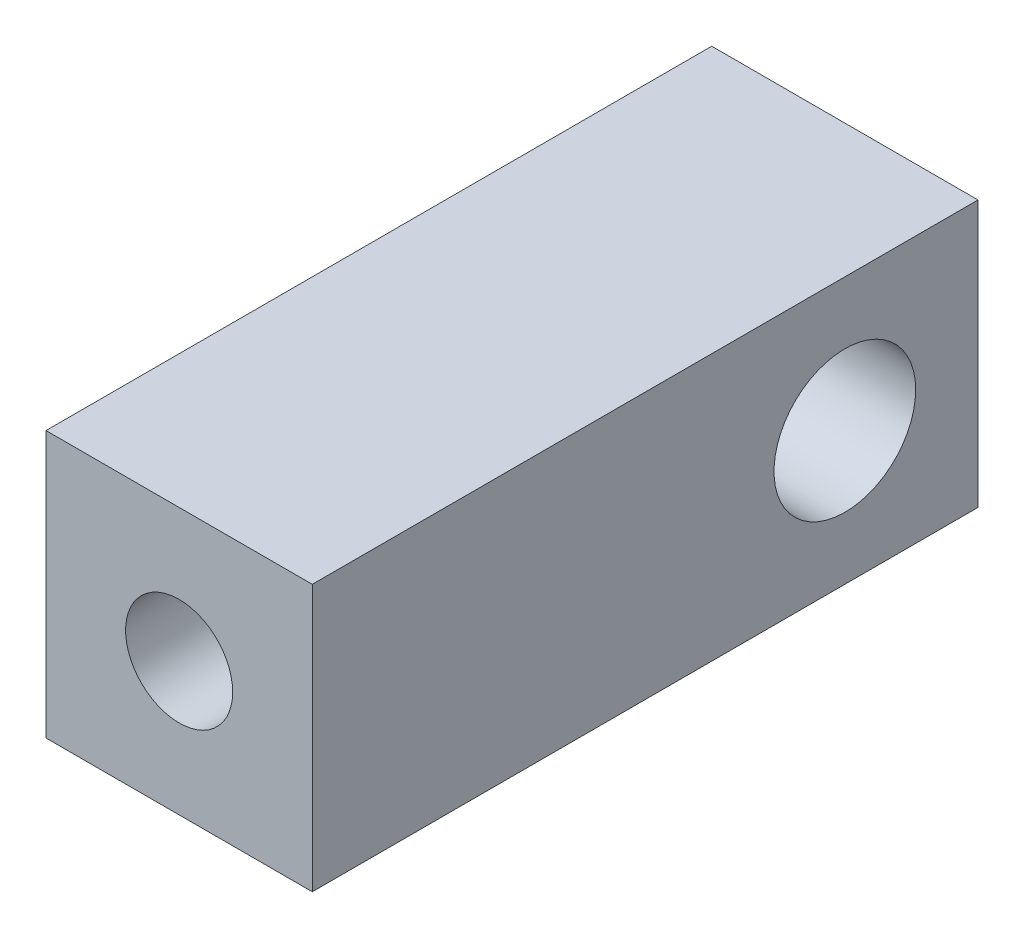
SolidWorks part; units mm, degrees
material "6061-T6 (SS)"
ref_plane "Front Plane" through (0, 0, 0) normal (0, 0, 1) x (1, 0, 0)
ref_plane "Top Plane" through (0, 0, 0) normal (0, 1, 0) x (1, 0, 0)
ref_plane "Right Plane" through (0, 0, 0) normal (1, 0, 0) x (0, 0, -1)
sketch "Sketch1" plane through (0, 0, 0) normal (1, 0, 0) x (0, 0, -1)
  line L1 (0, 0) -> (31.75, 0)
  line L2 (0, 0) -> (0, 12.7)
  line L3 (0, 12.7) -> (31.75, 12.7)
  line L4 (31.75, 0) -> (31.75, 12.7)
  dimension "D1" = 12.7
  dimension "D2" = 31.75
extrude "Boss-Extrude1" add sketch "Sketch1" along normal blind 12.7
hole_wizard "1/4-20 Tapped Hole1" positions "Sketch2" profile "Sketch3" tap size "1/4-20" standard "ANSI Inch"
sketch "Sketch2" plane through (0, 0, 0) normal (0, 0, 1) x (1, 0, 0)
  line L0 (0, 0) -> (12.7, 12.7) construction
  point P0 (6.35, 6.35)
cosmetic thread "Hole Thread1" parameters "D1"=12.7, "D2"=6.35
sketch "Sketch3" plane through (6.35, 6.35, 0) normal (1, 0, 0) x (0, -1, 0)
  line L0 (0, 0) -> (0, 18.0438)
  line L1 (0, 18.0438) -> (2.5527, 16.51)
  line L2 (2.5527, 16.51) -> (2.5527, 0)
  line L5 (2.5527, 0) -> (0, 0)
  line L10 (0, 18.0438) -> (-2.5527, 16.51) construction
  line L11 (0, -6.35) -> (0, 107.95) construction
  dimension "Tap Drill Dia." = 5.1054
  dimension "Tap Drill Depth" = 16.51
  dimension "Drill Angle" = 118
sketch "Sketch4" plane through (12.7, 0, 0) normal (1, 0, 0) x (0, 0, -1)
  line L0 (31.75, 0) -> (31.75, 12.7) construction
  line L1 (0, 12.7) -> (0, 0) construction
  circle A0 centre (25.4, 6.35) radius 3.3782
  point P7 (0, 6.35)
  dimension "D1" = 6.35
  dimension "D2" = 6.7564
extrude "Cut-Extrude1" cut sketch "Sketch4" against normal through all
